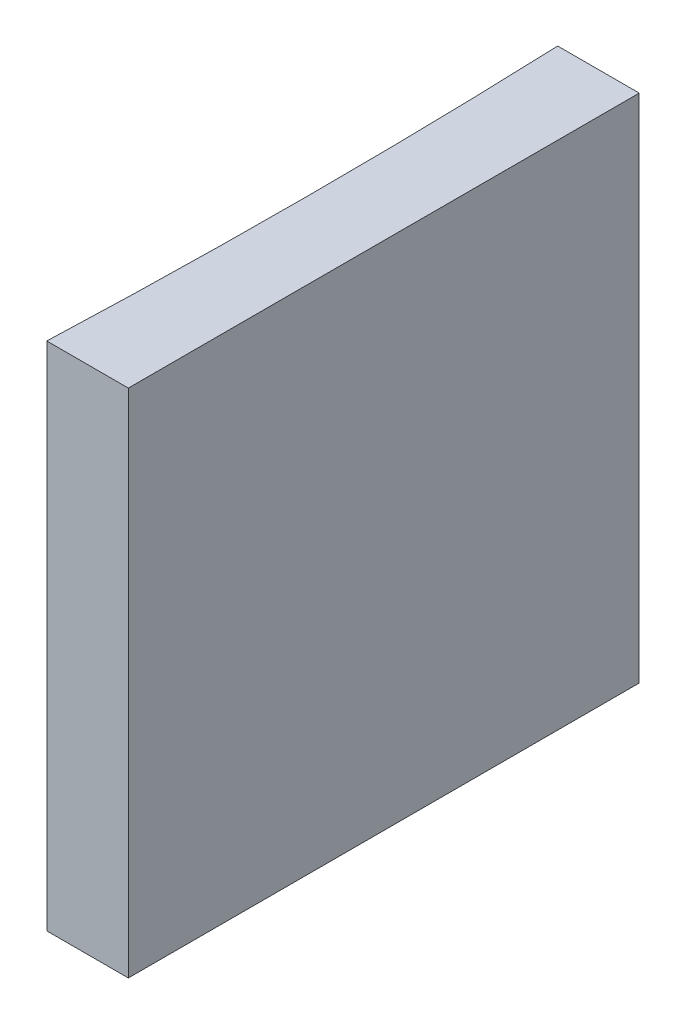
SolidWorks part; units mm, degrees
ref_plane "前视基准面" through (0, 0, 0) normal (0, 0, 1) x (1, 0, 0)
ref_plane "上视基准面" through (0, 0, 0) normal (0, 1, 0) x (1, 0, 0)
ref_plane "右视基准面" through (0, 0, 0) normal (1, 0, 0) x (0, 0, -1)
sketch "草图1" plane through (0, 0, 0) normal (0, 1, 0) x (1, 0, 0)
  line L0 (0, 0) -> (0, -20)
  line L1 (0, 0) -> (-3.1935, 0)
  line L2 (0, -20) -> (-3.1935, -20)
  line L3 (8.2336, -10) -> (-10.4405, -10) construction
  arc A0 (-3.1935, -20) -> (-3.1935, 0) centre (-261.5, -10) ccw
  point P7 (-3, -10)
  point P8 (0, -10)
  dimension "D2" = 258.5
  dimension "D3" = 3
  dimension "D1" = 20
extrude "凸台-拉伸1" add sketch "草图1" along normal blind 20
